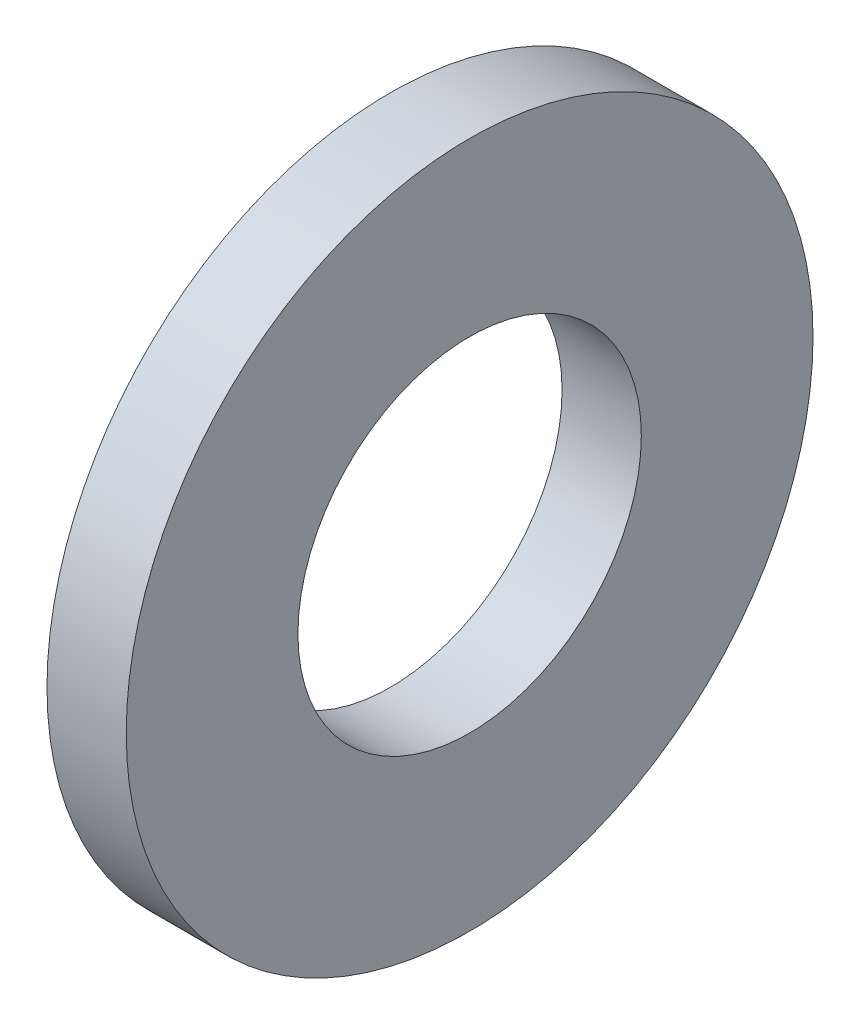
SolidWorks part; units mm, degrees
material "Nylon 101"
ref_plane "Front Plane" through (0, 0, 0) normal (0, 0, 1) x (1, 0, 0)
ref_plane "Top Plane" through (0, 0, 0) normal (0, 1, 0) x (1, 0, 0)
ref_plane "Right Plane" through (0, 0, 0) normal (1, 0, 0) x (0, 0, -1)
sketch "Sketch1" plane through (0, 0, 0) normal (1, 0, 0) x (0, 0, -1)
  circle A0 centre (0, 0) radius 3.9624
  circle A1 centre (0, 0) radius 1.9812
  dimension "OD" = 7.9248
  dimension "ID" = 3.9624
extrude "Boss-Extrude1" add sketch "Sketch1" along normal blind 0.9144
